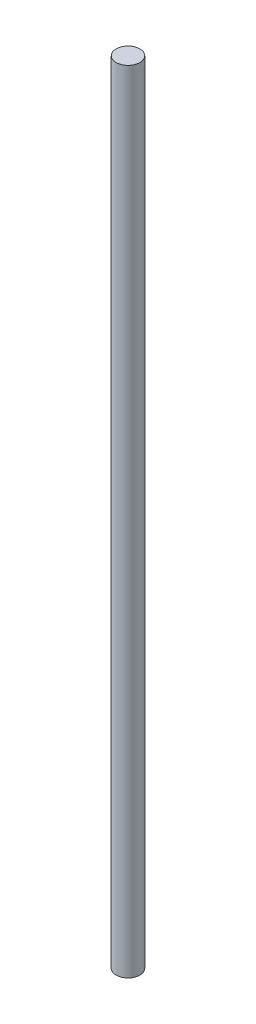
SolidWorks part; units mm, degrees
ref_plane "Front" through (0, 0, 0) normal (0, 0, 1) x (1, 0, 0)
ref_plane "Top" through (0, 0, 0) normal (0, 1, 0) x (1, 0, 0)
ref_plane "Right" through (0, 0, 0) normal (1, 0, 0) x (0, 0, -1)
sketch "Sketch1" plane through (0, 0, 0) normal (0, 1, 0) x (1, 0, 0)
  circle A0 centre (0, 0) radius 1.5
  dimension "D1" = 3
extrude "Boss-Extrude1" add sketch "Sketch1" along normal blind 100
